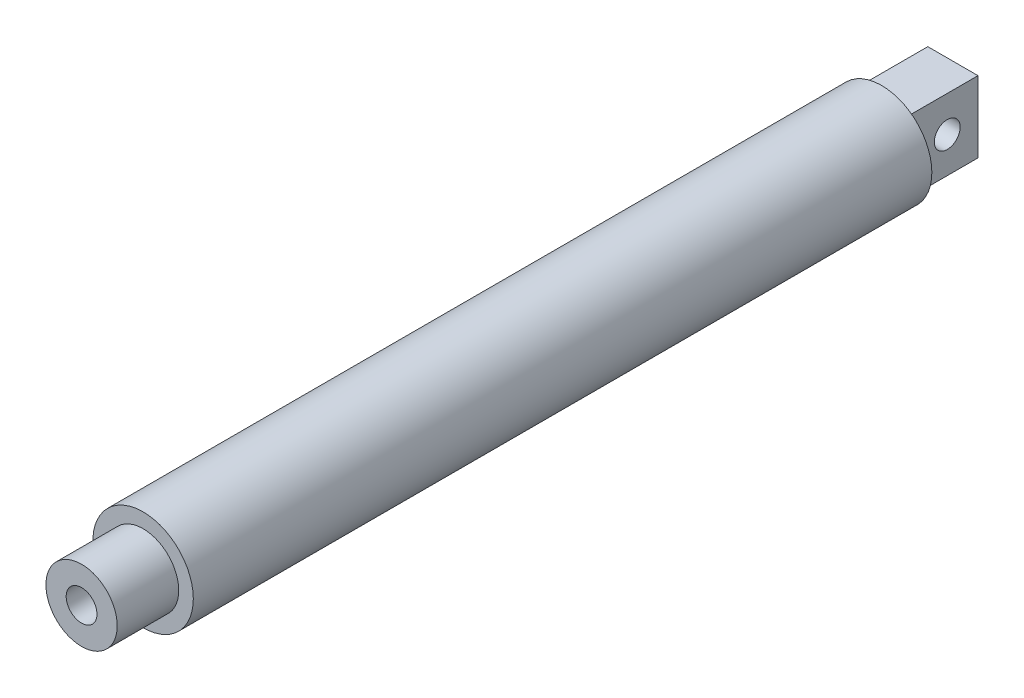
SolidWorks part; units mm, degrees
material "6061-T6 (SS)"
ref_plane "Front Plane" through (0, 0, 0) normal (0, 0, 1) x (1, 0, 0)
ref_plane "Top Plane" through (0, 0, 0) normal (0, 1, 0) x (1, 0, 0)
ref_plane "Right Plane" through (0, 0, 0) normal (1, 0, 0) x (0, 0, -1)
sketch "Sketch1" plane through (0, 0, 0) normal (0, 0, 1) x (1, 0, 0)
  circle A0 centre (0, 0) radius 7.874
  dimension "D1" = 15.748
extrude "Boss-Extrude1" add sketch "Sketch1" along normal blind 115.824
sketch "Sketch2" plane through (0, 0, 115.824) normal (0, 0, 1) x (1, 0, 0)
  circle A0 centre (0, 0) radius 5.588
  dimension "D1" = 11.176
extrude "Boss-Extrude2" add sketch "Sketch2" along normal blind 9.652
sketch "Sketch3" plane through (0, 0, 0) normal (0, 0, -1) x (-1, 0, 0)
  line L1 (-3.937, -5.588) -> (3.937, -5.588)
  line L2 (-3.937, -5.588) -> (-3.937, 5.588)
  line L3 (-3.937, 5.588) -> (3.937, 5.588)
  line L4 (3.937, -5.588) -> (3.937, 5.588)
  line L5 (-3.937, -5.588) -> (3.937, 5.588) construction
  line L6 (-3.937, 5.588) -> (3.937, -5.588) construction
  point P0 (0, 0)
  dimension "D1" = 7.874
  dimension "D2" = 11.176
extrude "Boss-Extrude3" add sketch "Sketch3" along normal blind 11.176
sketch "Sketch4" plane through (3.937, 0, 0) normal (1, 0, 0) x (0, 0, -1)
  line L0 (0, 0) -> (6.35, 0) construction
  line L1 (0, 5.588) -> (0, -5.588) construction
  circle A0 centre (6.35, 0) radius 2.032
  dimension "D1" = 4.064
  dimension "D2" = 6.35
extrude "Cut-Extrude1" cut sketch "Sketch4" against normal through all
sketch "Sketch5" plane through (0, 0, 125.476) normal (0, 0, 1) x (1, 0, 0)
  circle A0 centre (0, 0) radius 2.413
  dimension "D1" = 4.826
extrude "Cut-Extrude2" cut sketch "Sketch5" against normal blind 114.3
equation "\"A\"= 4.56"
equation "\"CylinderBody\"= \"A\" - .25 - .38"
equation "\"D1@Boss-Extrude1\"= \"A\""
